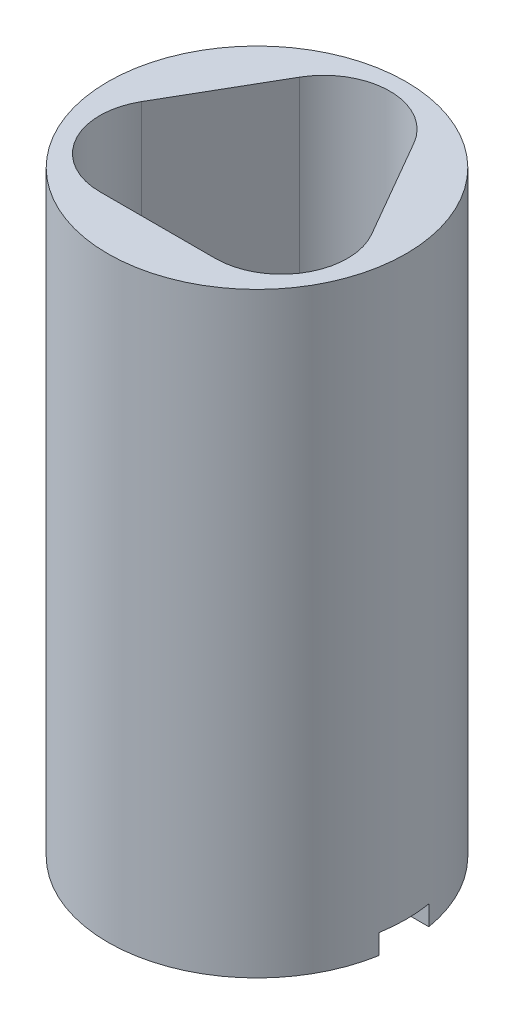
SolidWorks part; units mm, degrees
material "Stainless Steel"
ref_plane "Front Plane" through (0, 0, 0) normal (0, 0, 1) x (1, 0, 0)
ref_plane "Top Plane" through (0, 0, 0) normal (0, 1, 0) x (1, 0, 0)
ref_plane "Right Plane" through (0, 0, 0) normal (1, 0, 0) x (0, 0, -1)
sketch "Sketch1" plane through (0, 0, 0) normal (0, 1, 0) x (1, 0, 0)
  circle A0 centre (0, 0) radius 4.7625
  dimension "D1" = 9.525
extrude "Extrude1" add sketch "Sketch1" along normal blind 19.05
cosmetic thread "Cosmetic Thread1" parameters "D2"=8.89
sketch "Sketch2" plane through (0, 19.05, 0) normal (0, 1, 0) x (1, 0, 0)
  circle A0 centre (0, 0) radius 3.0607
  dimension "D1" = 6.1214
extrude "Cut-Extrude1" cut sketch "Sketch2" against normal blind 10.414
sketch "Sketch3" plane through (0, 0, 0) normal (0, -1, 0) x (1, 0, 0)
  circle A0 centre (0, 0) radius 3.4925
  dimension "D1" = 6.985
extrude "Cut-Extrude2" cut sketch "Sketch3" against normal blind 0.635
sketch "Sketch8" plane through (0, 19.05, 0) normal (0, 1, 0) x (1, 0, 0)
  line L1 (-1.8258, 3.1877) -> (-3.6735, -0.0127)
  line L2 (-1.8478, -3.175) -> (1.8478, -3.175)
  line L3 (3.6735, -0.0127) -> (1.8258, 3.1877)
  circle A0 centre (0, 0) radius 3.175 construction
  arc A1 (1.8478, -3.175) -> (3.6735, -0.0127) centre (1.8478, -1.0668) ccw
  arc A2 (-1.8258, 3.1877) -> (1.8258, 3.1877) centre (0, 2.1336) cw
  arc A3 (-3.6735, -0.0127) -> (-1.8478, -3.175) centre (-1.8478, -1.0668) ccw
  dimension "D2" = 2.1082
  dimension "D1" = 3.175
extrude "Cut-Extrude5" cut sketch "Sketch8" against normal blind 6.35
sketch "Sketch5" plane through (0, 0.635, 0) normal (0, -1, 0) x (1, 0, 0)
  line L0 (-3.4925, 0) -> (3.4925, 0) construction
  line L1 (0, 3.4925) -> (0, -3.4925) construction
  circle A0 centre (0, 0) radius 3.4925 construction
  circle A1 centre (0, 0) radius 3.4925 construction
hole_wizard "9/64 (0.14063) Diameter Hole1" positions "3DSketch1" profile "Sketch6" hole size "9/64" standard "Ansi Inch" end condition through all
sketch3d "3DSketch1"
  line L0 (-3.4925, 0.635, 0) -> (3.4925, 0.635, 0) construction
  line L1 (0, 0.635, 3.4925) -> (0, 0.635, -3.4925) construction
  point P0 (0, 0.635, 0)
sketch "Sketch6" plane through (0, 0.635, 0) normal (1, 0, 0) x (0, 0, -1)
  line L0 (0, 0) -> (0, 18.415)
  line L1 (0, 18.415) -> (1.7856, 18.415)
  line L2 (1.7856, 18.415) -> (1.7856, 0)
  line L5 (1.7856, 0) -> (0, 0)
  line L11 (0, -6.35) -> (0, 107.95) construction
  dimension "Thru Hole Dia." = 3.5712
  dimension "Thru Hole Depth" = 18.415
sketch "Sketch7" plane through (0, 0, 0) normal (0, -1, 0) x (1, 0, 0)
  line L1 (4.7625, -0.7937) -> (-4.7625, -0.7937)
  line L2 (4.7625, -0.7937) -> (4.7625, 0.7937)
  line L3 (4.7625, 0.7937) -> (-4.7625, 0.7937)
  line L4 (-4.7625, -0.7937) -> (-4.7625, 0.7937)
  line L5 (4.7625, -0.7937) -> (-4.7625, 0.7937) construction
  line L6 (4.7625, 0.7937) -> (-4.7625, -0.7937) construction
  circle A0 centre (0, 0) radius 4.7625 construction
  point P0 (0, 0)
  dimension "D1" = 1.5875
extrude "Cut-Extrude4" cut sketch "Sketch7" against normal up to surface (0.635 mm away) up to face at (0, 0.635, -1.7856)
